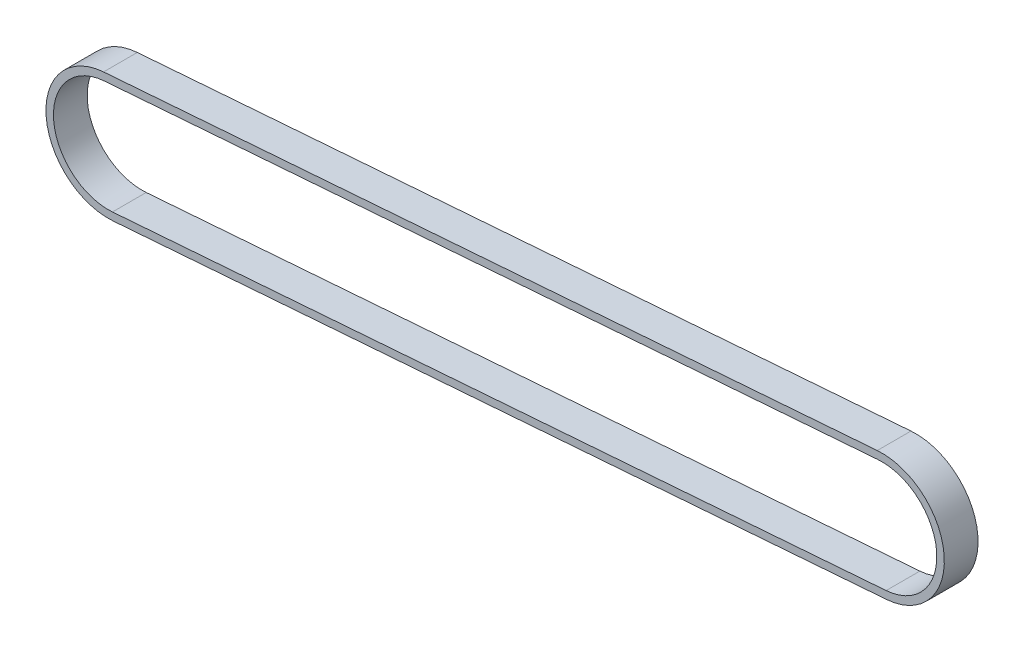
SolidWorks part; units mm, degrees
ref_plane "Front Plane" through (0, 0, 0) normal (0, 0, 1) x (1, 0, 0)
ref_plane "Top Plane" through (0, 0, 0) normal (0, 1, 0) x (1, 0, 0)
ref_plane "Right Plane" through (0, 0, 0) normal (1, 0, 0) x (0, 0, -1)
sketch "Sketch2" plane through (0, 0, 0) normal (0, 0, 1) x (1, 0, 0)
  line L0 (0, 0) -> (1, 0) construction
  line L1 (0, 0) -> (0, 1) construction
  line L2 (-1.6342, 18.5724) -> (259.4591, 38.4755)
  line L3 (262.2714, 1.5825) -> (1.1782, -18.3206)
  arc A0 (1.1782, -18.3206) -> (-1.6342, 18.5724) centre (-0.228, 0.1259) cw
  arc A1 (259.4591, 38.4755) -> (262.2714, 1.5825) centre (260.8653, 20.029) cw
sketch3d "3DSketch1"
  line L2 (-1.6342, 18.5724, 0.3827) -> (259.4591, 38.4755, 0.3827)
  line L3 (262.2714, 1.5825, 0.3827) -> (1.1782, -18.3206, 0.3827)
  line L4 (-1.6342, 18.5724, 0.3827) -> (259.4591, 38.4755, 0.3827)
  line L5 (262.2714, 1.5825, 0.3827) -> (1.1782, -18.3206, 0.3827)
  arc A2 (259.4591, 38.4755, 0.3827) -> (262.2714, 1.5825, 0.3827) centre (260.8653, 20.029, 0.3827) ccw
  arc A3 (1.1782, -18.3206, 0.3827) -> (-1.6342, 18.5724, 0.3827) centre (-0.228, 0.1259, 0.3827) ccw
  arc A4 (259.4591, 38.4755, 0.3827) -> (262.2714, 1.5825, 0.3827) centre (260.8653, 20.029, 0.3827) ccw
  arc A5 (1.1782, -18.3206, 0.3827) -> (-1.6342, 18.5724, 0.3827) centre (-0.228, 0.1259, 0.3827) ccw
  point P6 (260.8653, 20.029, -18.1173)
  point P10 (-0.228, 0.1259, -18.1173)
  point P12 (260.8653, 20.029, -18.1173)
  point P13 (-0.228, 0.1259, -18.1173)
  dimension "D1" = 0
extrude "Extrude-Thin2" add sketch "Sketch2" along normal up to surface (11.3827 mm away) thin thin type one direction wall 2.54
